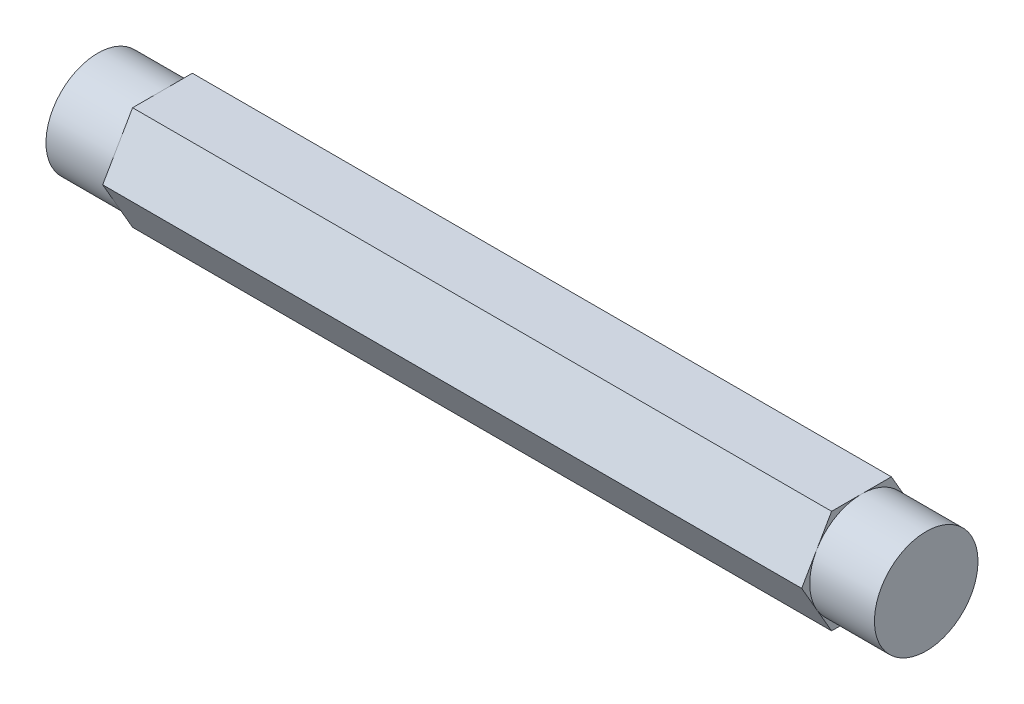
SolidWorks part; units mm, degrees
material "7075-T6 (SN)"
ref_plane "Front Plane" through (0, 0, 0) normal (0, 0, 1) x (1, 0, 0)
ref_plane "Top Plane" through (0, 0, 0) normal (0, 1, 0) x (1, 0, 0)
ref_plane "Right Plane" through (0, 0, 0) normal (1, 0, 0) x (0, 0, -1)
sketch "Sketch2" plane through (0, 0, 0) normal (1, 0, 0) x (0, 0, -1)
  line L1 (7.3323, 0) -> (3.6662, 6.35)
  line L2 (3.6662, 6.35) -> (-3.6662, 6.35)
  line L3 (-3.6662, 6.35) -> (-7.3323, 0)
  line L4 (-7.3323, 0) -> (-3.6662, -6.35)
  line L5 (-3.6662, -6.35) -> (3.6662, -6.35)
  line L6 (3.6662, -6.35) -> (7.3323, 0)
  circle A0 centre (0, 0) radius 6.35 construction
  dimension "D1" = 12.7
extrude "Boss-Extrude1" add sketch "Sketch2" along normal mid plane 101.6
sketch "Sketch3" plane through (50.8, 0, 0) normal (1, 0, 0) x (0, 0, -1)
  circle A0 centre (0, 0) radius 6.35
  dimension "D1" = 12.7
extrude "Cut-Extrude-Thin1" cut sketch "Sketch3" against normal blind 7.9375 thin
mirror "Mirror1" about plane through (0, 0, 0) normal (1, 0, 0) of "Cut-Extrude-Thin1"
hole_wizard "1/4-20 Tapped Hole1" [suppressed] positions "3DSketch1" profile "Sketch5" tap size "1/4-20" standard "ANSI Inch"
sketch3d "3DSketch1"
  line L0 (42.8625, 0, 0) -> (50.8, 0, 0) construction
  line L1 (-42.8625, 0, 0) -> (-50.8, 0, 0) construction
  point P0 (50.8, 0, 0)
  point P4 (-50.8, 0, 0)
sketch "Sketch5" plane through (50.8, 0, 0) normal (0, 1, 0) x (0, 0, -1)
  line L0 (0, 0) -> (0, 18.0438)
  line L1 (0, 18.0438) -> (2.5527, 16.51)
  line L2 (2.5527, 16.51) -> (2.5527, 0)
  line L5 (2.5527, 0) -> (0, 0)
  line L10 (0, 18.0438) -> (-2.5527, 16.51) construction
  line L11 (0, -6.35) -> (0, 107.95) construction
  dimension "Tap Drill Dia." = 5.1054
  dimension "Tap Drill Depth" = 16.51
  dimension "Drill Angle" = 118
cosmetic thread "Hole Thread1" [suppressed] parameters "D1"=12.7, "D2"=6.35
cosmetic thread "Hole Thread2" [suppressed] parameters "D1"=12.7, "D2"=6.35
